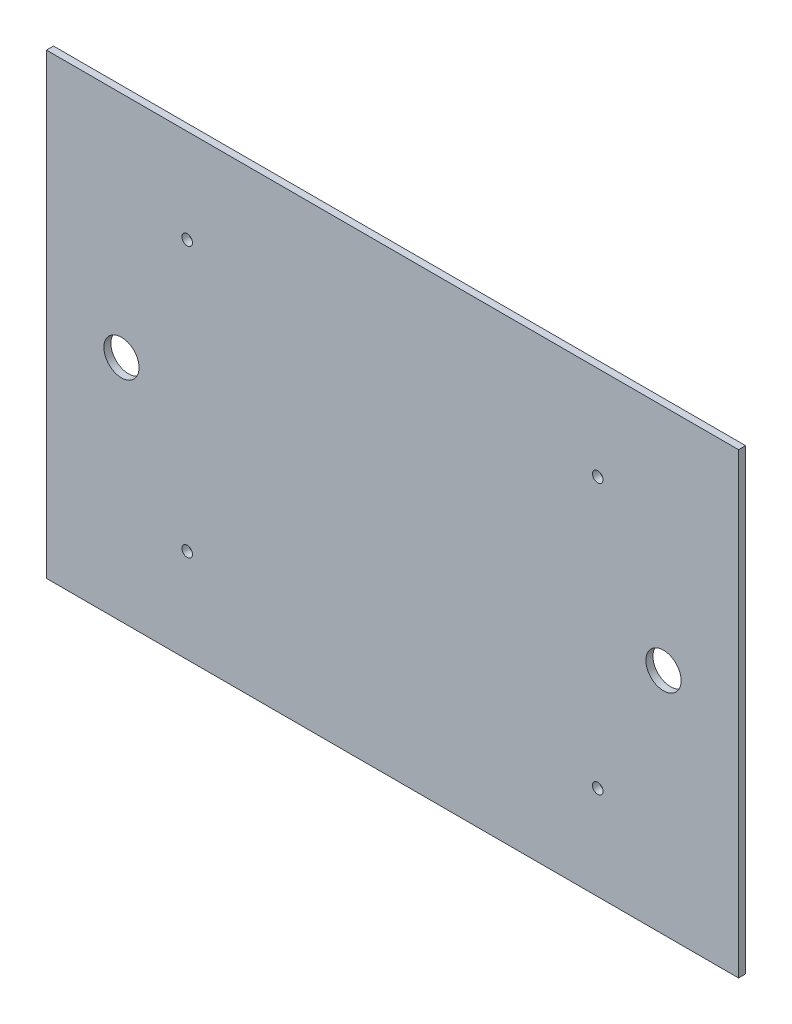
SolidWorks part; units mm, degrees
ref_plane "Plan de face" through (0, 0, 0) normal (0, 0, 1) x (1, 0, 0)
ref_plane "Plan de dessus" through (0, 0, 0) normal (0, 1, 0) x (1, 0, 0)
ref_plane "Plan de droite" through (0, 0, 0) normal (1, 0, 0) x (0, 0, -1)
sketch "Esquisse1" plane through (0, 0, 0) normal (0, 0, 1) x (1, 0, 0)
  line L0 (147.5, 0) -> (147.5, -195) construction
  line L1 (0, 0) -> (295, 0)
  line L2 (0, 0) -> (0, -195)
  line L3 (0, -195) -> (295, -195)
  line L4 (295, 0) -> (295, -195)
  line L5 (0, -97.5) -> (295, -97.5) construction
  line L6 (32, -74.163) -> (32, -119.0922) construction
  line L7 (263, -74.163) -> (263, -119.0922) construction
  circle A0 centre (60, -40) radius 2.25
  circle A1 centre (235, -40) radius 2.25
  circle A2 centre (235, -155) radius 2.25
  circle A3 centre (60, -155) radius 2.25
  circle A4 centre (32, -97.5) radius 7.5
  circle A5 centre (263, -97.5) radius 7.5
  dimension "D3" = 4.5
  dimension "D7" = 15
  dimension "D1" = 295
  dimension "D2" = 195
  dimension "D4" = 60
  dimension "D5" = 40
  dimension "D6" = 32
extrude "Boss.-Extru.1" add sketch "Esquisse1" along normal blind 3
